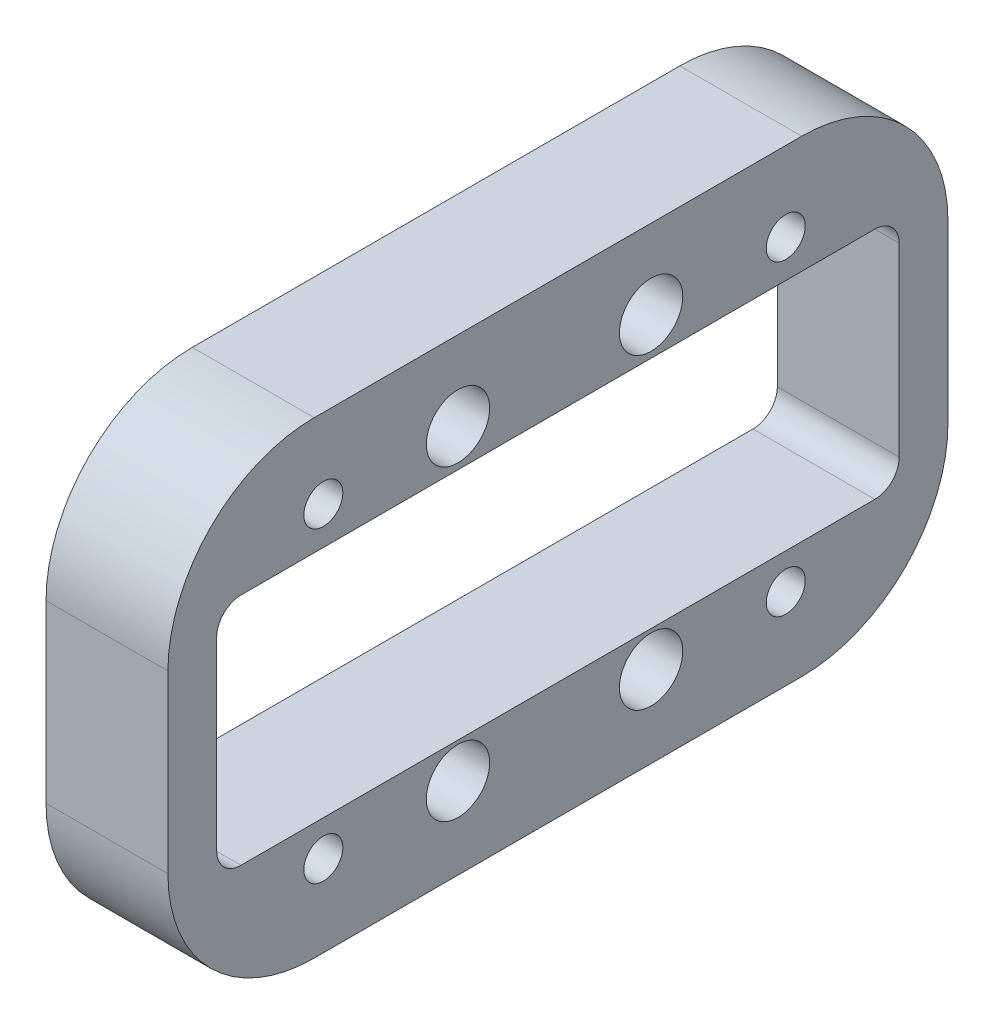
SolidWorks part; units mm, degrees
ref_plane "前视基准面" through (0, 0, 0) normal (0, 0, 1) x (1, 0, 0)
ref_plane "上视基准面" through (0, 0, 0) normal (0, 1, 0) x (1, 0, 0)
ref_plane "右视基准面" through (0, 0, 0) normal (1, 0, 0) x (0, 0, -1)
sketch "草图1" plane through (0, 0, 0) normal (1, 0, 0) x (0, 0, -1)
  line L1 (-61.9415, 62.3233) -> (98.0585, 62.3233)
  line L2 (-61.9415, 62.3233) -> (-61.9415, -33.6767)
  line L3 (-61.9415, -33.6767) -> (98.0585, -33.6767)
  line L4 (98.0585, 62.3233) -> (98.0585, -33.6767)
  line L5 (-51.9415, 38.3233) -> (88.0585, 38.3233)
  line L6 (-51.9415, 38.3233) -> (-51.9415, -9.6767)
  line L7 (-51.9415, -9.6767) -> (88.0585, -9.6767)
  line L8 (88.0585, 38.3233) -> (88.0585, -9.6767)
  circle A0 centre (-2.4436, 46.0633) radius 4
  circle A1 centre (37.163, 46.0633) radius 4
  circle A2 centre (-2.4436, -16.9444) radius 4
  circle A3 centre (37.163, -16.9444) radius 4
  circle A4 centre (64.7846, 46.0633) radius 4
  circle A5 centre (-30.0636, -16.9444) radius 4
  circle A6 centre (64.7846, -16.9444) radius 4
  circle A7 centre (-30.0636, 46.0633) radius 4
  dimension "D1" = 16.9444
  dimension "D2" = 62.3233
  dimension "D5" = 27.62
  dimension "D6" = 27.6216
  dimension "D7" = 27.62
  dimension "D8" = 27.6216
  dimension "D9" = 39.6067
  dimension "D10" = 39.6067
  dimension "D11" = 37.163
  dimension "D3" = 160
  dimension "D4" = 98.0585
  dimension "D12" = 48
  dimension "D13" = 140
  dimension "D14" = 24
  dimension "D15" = 96
  dimension "D16" = 10
extrude "凸台-拉伸1" add sketch "草图1" against normal blind 25
fillet "圆角1" radius 30 4 edges at (-12.5, -33.6767, 61.9415) (-12.5, 62.3233, 61.9415) (-12.5, 62.3233, -98.0585) (-12.5, -33.6767, -98.0585)
fillet "圆角2" radius 5 4 edges at (-12.5, -9.6767, 51.9415) (-12.5, 38.3233, 51.9415) (-12.5, -9.6767, -88.0585) (-12.5, 38.3233, -88.0585)
sketch "草图11" plane through (0, 0, 0) normal (1, 0, 0) x (0, 0, -1)
  circle A0 centre (37.163, 46.0633) radius 6.4982
  circle A1 centre (-2.4436, 46.0633) radius 6.5
  circle A2 centre (37.163, -16.9444) radius 6.5
  circle A3 centre (-2.4436, -16.9444) radius 6.5
extrude "切除-拉伸1" cut sketch "草图11" against normal blind 15
